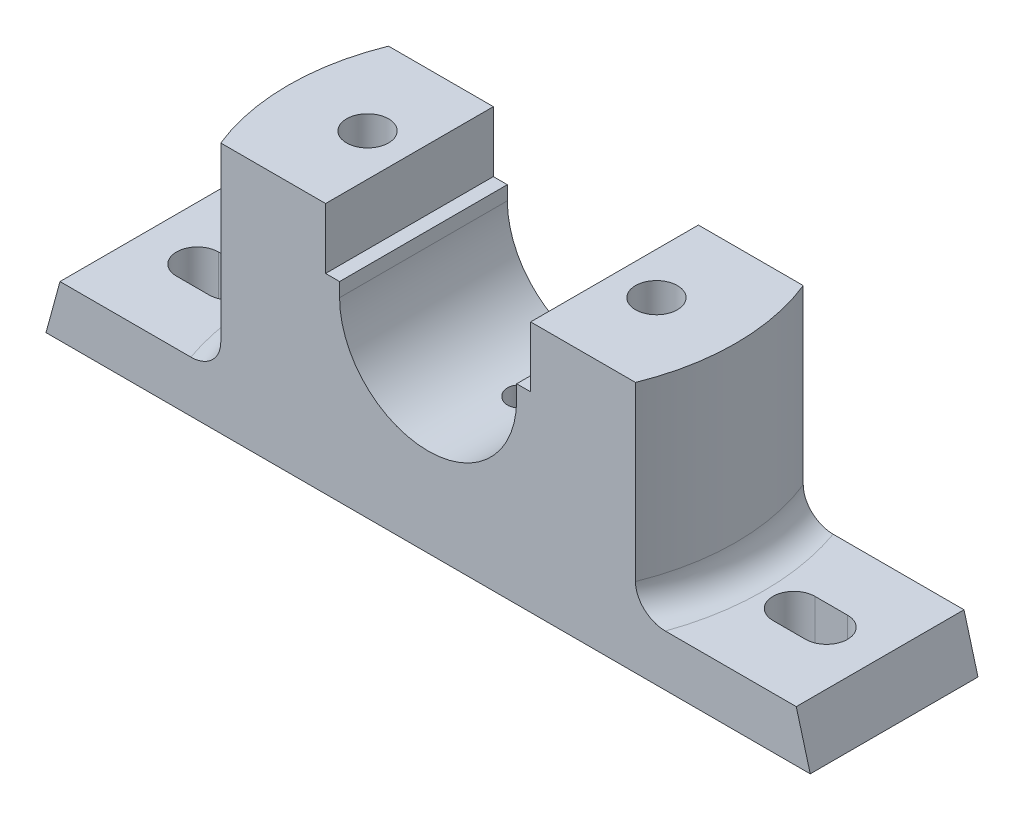
SolidWorks part; units mm, degrees
ref_plane "Front" through (0, 0, 0) normal (0, 0, 1) x (1, 0, 0)
ref_plane "Top" through (0, 0, 0) normal (0, 1, 0) x (1, 0, 0)
ref_plane "Right" through (0, 0, 0) normal (1, 0, 0) x (0, 0, -1)
sketch "Sketch2" plane through (0, 0, 0) normal (0, 0, 1) x (1, 0, 0)
  line L0 (0, 0) -> (0, 61.8981) construction
  line L1 (-82, 0) -> (82, 0)
  line L2 (82, 0) -> (79, 11)
  line L3 (79, 11) -> (50, 11)
  line L4 (50, 11) -> (50, 54)
  line L5 (50, 54) -> (22, 54)
  line L6 (22, 54) -> (22, 41)
  line L7 (22, 41) -> (19, 41)
  line L8 (19, 41) -> (19, 38)
  line L9 (-82, 0) -> (-79, 11)
  line L10 (-79, 11) -> (-50, 11)
  line L11 (-50, 11) -> (-50, 54)
  line L12 (-50, 54) -> (-22, 54)
  line L13 (-22, 54) -> (-22, 41)
  line L14 (-22, 41) -> (-19, 41)
  line L15 (-19, 41) -> (-19, 38)
  arc A0 (19, 38) -> (-19, 38) centre (0, 38) cw
  dimension "D9" = 19
  dimension "D1" = 164
  dimension "D2" = 3
  dimension "D3" = 11
  dimension "D4" = 13
  dimension "D5" = 16
  dimension "D6" = 50
  dimension "D7" = 44
  dimension "D8" = 38
  dimension "D10" = 54
extrude "Boss-Extrude1" add sketch "Sketch2" along normal mid plane 36
sketch "Sketch3" plane through (0, 54, 0) normal (0, 1, 0) x (1, 0, 0)
  line L0 (-22, 18) -> (-50, 18) construction
  line L1 (-22, -18) -> (-50, -18) construction
  line L2 (-50, -18) -> (-50, 18) construction
  line L3 (-44.4972, -18) -> (-50, -18)
  line L4 (-50, -18) -> (-50, 18)
  line L5 (-44.4972, 18) -> (-50, 18)
  arc A0 (-44.4972, 18) -> (-44.4972, -18) centre (0, 0) ccw
  dimension "D1" = 48
extrude "Cut-Extrude2" cut sketch "Sketch3" against normal blind 43
sketch "Sketch4" plane through (0, 11, 0) normal (0, 1, 0) x (1, 0, 0)
  line L0 (-67.5, 0) -> (-60.5, 0) construction
  line L1 (-67.5, 4.5) -> (-60.5, 4.5)
  line L2 (-67.5, -4.5) -> (-60.5, -4.5)
  arc A0 (-67.5, 4.5) -> (-67.5, -4.5) centre (-67.5, 0) ccw
  arc A1 (-60.5, -4.5) -> (-60.5, 4.5) centre (-60.5, 0) ccw
  point P3 (-64, 0)
  dimension "D2" = 16
  dimension "D1" = 64
  dimension "D3" = 9
extrude "Cut-Extrude3" cut sketch "Sketch4" against normal blind 11
sketch "Sketch6" plane through (0, 0, 0) normal (0, -1, 0) x (1, 0, 0)
  line L1 (-41, -10) -> (-21, -10)
  line L2 (-41, -10) -> (-41, 10)
  line L3 (-41, 10) -> (-21, 10)
  line L4 (-21, -10) -> (-21, 10)
  line L5 (-41, -10) -> (-21, 10) construction
  line L6 (-41, 10) -> (-21, -10) construction
  point P0 (-31, 0)
  dimension "D1" = 20
  dimension "D3" = 31
extrude "Cut-Extrude4" cut sketch "Sketch6" against normal blind 8
hole_wizard "Ø6.0mm Dowel Hole2" positions "Sketch11" profile "Sketch10" hole size "Ø6.0" standard "ANSI Metric"
sketch "Sketch11" plane through (0, 8, 0) normal (0, -1, 0) x (-1, 0, 0)
  line L1 (82, -18) -> (-82, -18) construction
  point P0 (31, 0)
  dimension "D1" = 31
  dimension "D2" = 18
sketch "Sketch10" plane through (-31, 8, 0) normal (1, 0, 0) x (0, 0, -1)
  line L0 (0, 0) -> (0, 48.7029)
  line L1 (0, 48.7029) -> (4.5, 45.999)
  line L2 (4.5, 45.999) -> (4.5, 0)
  line L5 (4.5, 0) -> (0, 0)
  line L10 (0, 48.7029) -> (-4.5, 45.999) construction
  line L11 (0, -6.35) -> (0, 107.95) construction
  dimension "Hole Dia." = 9
  dimension "Hole Depth" = 45.999
  dimension "Drill Angle" = 118
mirror "Mirror2" about plane through (0, 0, 0) normal (1, 0, 0) of "Cut-Extrude2", "Ø6.0mm Dowel Hole2", "Cut-Extrude3", "Cut-Extrude4"
fillet "Fillet1" radius 6 1 edges at (48, 11, 0)
fillet "Fillet2" radius 6 1 edges at (-48, 11, 0)
hole_wizard "Ø6.0mm Dowel Hole3" positions "3DSketch2" profile "Sketch13" hole size "Ø6.0" standard "ANSI Metric"
sketch3d "3DSketch2"
  point P8 (0, 19, -2.0494)
  dimension "D1" = 0
sketch "Sketch13" plane through (0, 19, -2.0494) normal (1, 0, 0) x (0, 0, 1)
  line L0 (0, 0) -> (0, 7.8026)
  line L1 (0, 7.8026) -> (3, 6)
  line L2 (3, 6) -> (3, 0)
  line L5 (3, 0) -> (0, 0)
  line L10 (0, 7.8026) -> (-3, 6) construction
  line L11 (0, -6.35) -> (0, 107.95) construction
  dimension "Hole Dia." = 6
  dimension "Hole Depth" = 6
  dimension "Drill Angle" = 118
